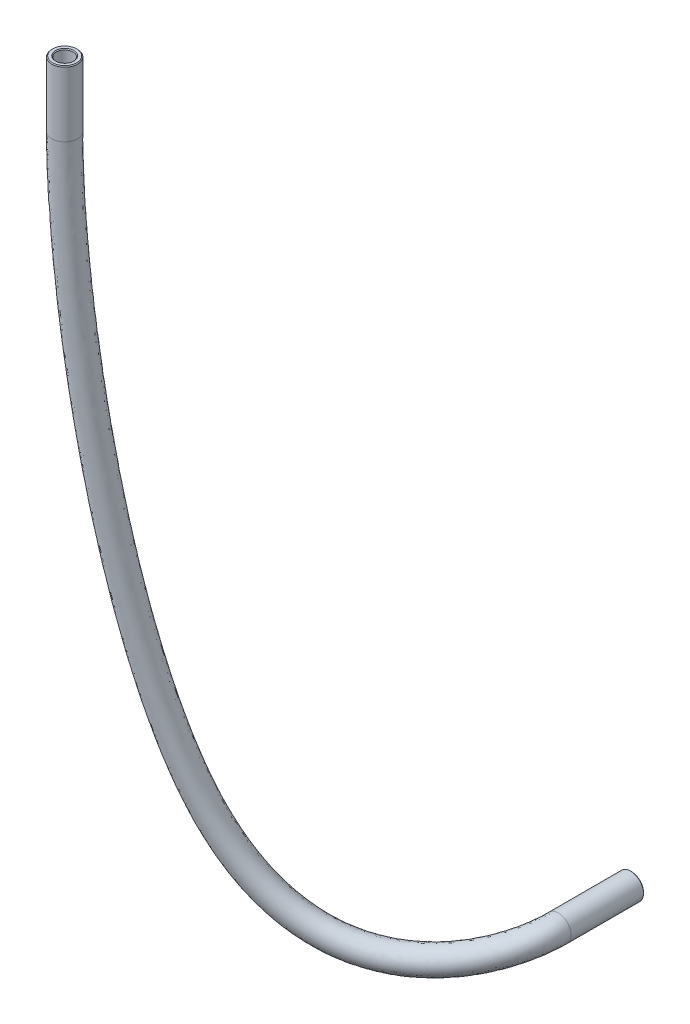
SolidWorks part; units mm, degrees
ref_plane "Front Plane" through (0, 0, 0) normal (0, 0, 1) x (1, 0, 0)
ref_plane "Top Plane" through (0, 0, 0) normal (0, 1, 0) x (1, 0, 0)
ref_plane "Right Plane" through (0, 0, 0) normal (1, 0, 0) x (0, 0, -1)
sketch "Sketch1" plane through (0, -117.5823, 0) normal (0, -1, 0) x (1, 0, 0)
  circle A0 centre (-150.0853, -17.525) radius 1.3
  circle A1 centre (-150.0853, -17.525) radius 2
  circle A2 centre (-150.0853, -17.525) radius 3.6 construction
  dimension "D1" = 2.6
  dimension "D2" = 4
sketch3d "3DSketch1"
  line L0 (-105.3988, -220.7938, -61.0875) -> (-105.3988, -220.7938, -49.6875)
  line L1 (-150.0853, -119.6823, -17.525) -> (-150.0853, -109.4823, -17.525)
  spline S0 degree 3 poles (-105.3988, -220.7938, -49.6875) (-105.3988, -220.7938, -39.9265) (-140.2449, -242.363, -25.0625) (-150.0853, -143.0968, -17.525) (-150.0853, -119.6823, -17.525) knots 0 0 0 0 0.546754 1 1 1 1
sweep "Sweep1" add profiles "Sketch1" path "3DSketch1"
chamfer "Chamfer1" distance 0.127 angle 45 4 edges at (-148.0853, -109.4823, -17.525) (-148.7853, -109.4823, -17.525) (-105.9437, -218.8695, -61.0875) (-105.753, -219.543, -61.0875)
